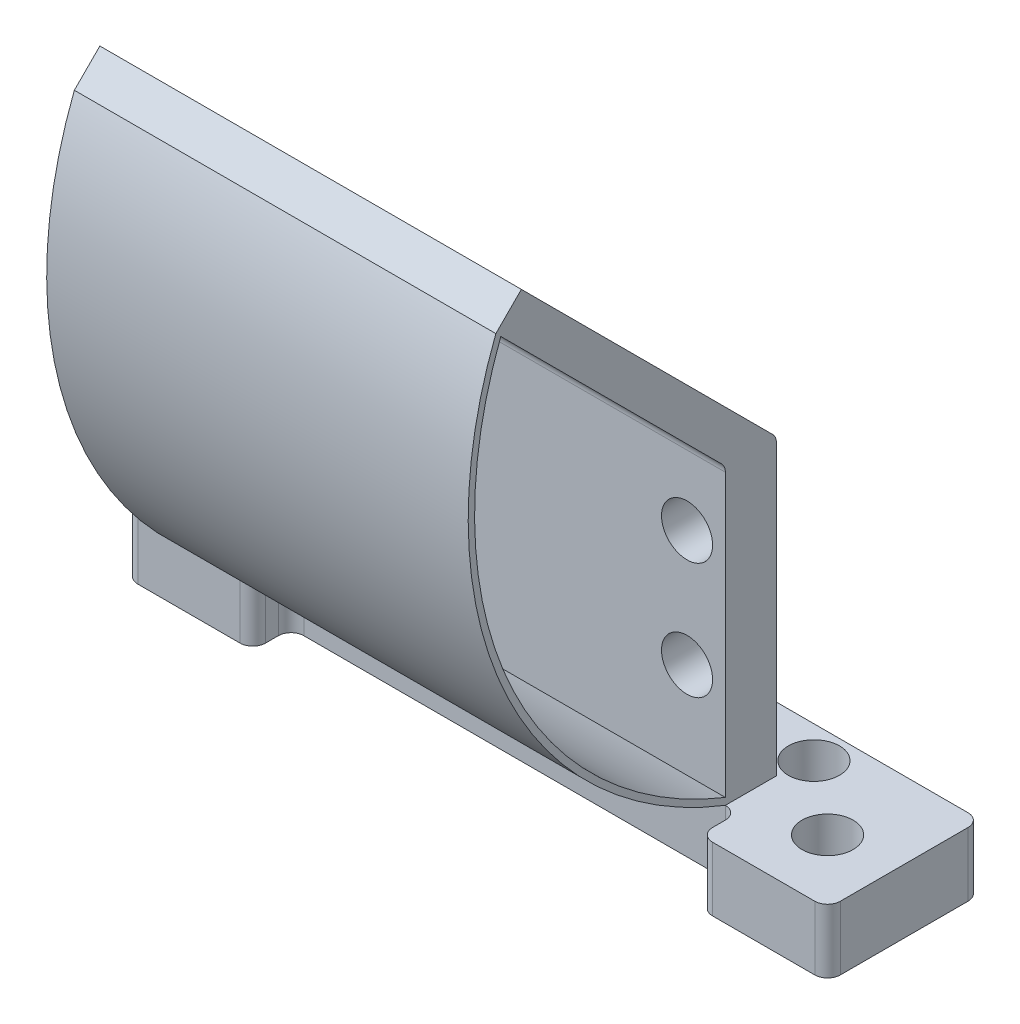
SolidWorks part; units mm, degrees
ref_plane "前视基准面" through (0, 0, 0) normal (0, 0, 1) x (1, 0, 0)
ref_plane "上视基准面" through (0, 0, 0) normal (0, 1, 0) x (1, 0, 0)
ref_plane "右视基准面" through (0, 0, 0) normal (1, 0, 0) x (0, 0, -1)
other "Configuration Table"
sketch "草图1" plane through (0, 0, 0) normal (0, 1, 0) x (1, 0, 0)
  line L0 (0.0338, 0) -> (0.0338, 2) construction
  line L2 (27.5338, -2.0074) -> (27.5338, 2.0025)
  line L4 (-27.4662, -1.9975) -> (-27.4662, 2.0025)
  line L5 (27.5338, -2.0074) -> (-27.4662, 2.0025) construction
  line L6 (27.5338, 2.0025) -> (-27.4662, -1.9975) construction
  line L7 (26.5338, -5) -> (18.5338, -5)
  line L8 (27.5338, -4) -> (27.5338, 4)
  line L9 (26.5338, 5) -> (18.5338, 5)
  line L10 (17.5338, -4) -> (17.5338, -3)
  line L11 (27.5338, -5) -> (17.5338, 5) construction
  line L12 (27.5338, 5) -> (17.5338, -5) construction
  line L13 (-26.4662, 5) -> (-18.4662, 5)
  line L14 (-17.4662, -4) -> (-17.4662, -3)
  line L15 (-26.4662, -5) -> (-18.4662, -5)
  line L16 (-27.4662, -4) -> (-27.4662, 4)
  line L17 (-17.4662, 3) -> (-17.4662, 4)
  line L18 (17.5338, 3) -> (17.5338, 4)
  line L19 (16.5338, -2) -> (-16.4662, -2)
  line L20 (16.5338, 2) -> (-16.4662, 2)
  arc A0 (18.5338, -5) -> (17.5338, -4) centre (18.5338, -4) cw
  arc A1 (26.5338, -5) -> (27.5338, -4) centre (26.5338, -4) ccw
  arc A2 (27.5338, 4) -> (26.5338, 5) centre (26.5338, 4) ccw
  arc A3 (18.5338, 5) -> (17.5338, 4) centre (18.5338, 4) ccw
  arc A4 (-18.4662, 5) -> (-17.4662, 4) centre (-18.4662, 4) cw
  arc A5 (-18.4662, -5) -> (-17.4662, -4) centre (-18.4662, -4) ccw
  arc A6 (-26.4662, -5) -> (-27.4662, -4) centre (-26.4662, -4) cw
  arc A7 (-27.4662, 4) -> (-26.4662, 5) centre (-26.4662, 4) cw
  arc A8 (-16.4662, -2) -> (-17.4662, -3) centre (-16.4662, -3) ccw
  arc A9 (-16.4662, 2) -> (-17.4662, 3) centre (-16.4662, 3) cw
  arc A10 (17.5338, 3) -> (16.5338, 2) centre (16.5338, 3) cw
  arc A11 (17.5338, -3) -> (16.5338, -2) centre (16.5338, -3) ccw
  point P0 (0, 0)
  point P6 (22.5338, 0)
  point P45 (-17.4662, 2)
  dimension "D6" = 1
  dimension "D7" = 1
  dimension "D1" = 55
  dimension "D2" = 4
  dimension "D3" = 5
  dimension "D4" = 10
  dimension "D5" = 10
extrude "凸台-拉伸2" add sketch "草图1" along normal blind 5 contours A11 L10 A0 L7 A1 L8 A2 L9 A3 L18 A10 L20 A9 L17 A4 L13 A7 L16 A6 L15 A5 L14 A8 L19
sketch "草图3" plane through (0, 0, 0) normal (0, -1, 0) x (1, 0, 0)
  line L0 (-16.4662, 2) -> (-16.4662, -2) construction
  line L1 (16.5338, 2) -> (16.5338, -2) construction
sketch "草图4" plane through (0, 5, 0) normal (0, 1, 0) x (1, 0, 0)
  line L0 (-16.4662, -2) -> (-16.4662, 2) construction
  line L1 (-16.4662, -2) -> (-16.4662, 2)
  line L2 (16.5338, -2) -> (16.5338, 2) construction
  line L3 (16.5338, -2) -> (-16.4662, -2) construction
  line L4 (16.5338, 2) -> (-16.4662, 2) construction
  line L5 (16.5338, -2) -> (16.5338, 2)
  line L6 (-16.4662, -2) -> (-16.4662, 2)
  line L7 (16.5338, -2) -> (-16.4662, -2)
  line L8 (16.5338, 2) -> (-16.4662, 2)
  line L10 (-16.4662, -2) -> (16.5338, -2)
  line L11 (-16.4662, -2) -> (-16.4662, 2)
  line L12 (-16.4662, -2) -> (16.5338, -2)
  line L13 (17.5338, -3) -> (17.5338, -4)
  line L14 (18.5338, -5) -> (26.5338, -5)
  line L15 (27.5338, -4) -> (27.5338, 4)
  line L16 (26.5338, 5) -> (18.5338, 5)
  line L17 (17.5338, 4) -> (17.5338, 3)
  line L18 (16.5338, 2) -> (-16.4662, 2)
  line L19 (-17.4662, 3) -> (-17.4662, 4)
  line L20 (-18.4662, 5) -> (-26.4662, 5)
  line L21 (-27.4662, 4) -> (-27.4662, -4)
  line L22 (-26.4662, -5) -> (-18.4662, -5)
  line L23 (-17.4662, -4) -> (-17.4662, -3)
  line L24 (-16.4662, -2) -> (16.5338, -2)
  line L25 (17.5338, -3) -> (17.5338, -4)
  line L26 (18.5338, -5) -> (26.5338, -5)
  line L27 (27.5338, -4) -> (27.5338, 4)
  line L28 (26.5338, 5) -> (18.5338, 5)
  line L29 (17.5338, 4) -> (17.5338, 3)
  line L30 (16.5338, 2) -> (-16.4662, 2)
  line L31 (-17.4662, 3) -> (-17.4662, 4)
  line L32 (-18.4662, 5) -> (-26.4662, 5)
  line L33 (-27.4662, 4) -> (-27.4662, -4)
  line L34 (-26.4662, -5) -> (-18.4662, -5)
  line L35 (-17.4662, -4) -> (-17.4662, -3)
  line L36 (-16.4662, 2) -> (16.5338, 2)
  line L37 (16.5338, -2) -> (16.5338, 2)
  arc A12 (17.5338, -3) -> (16.5338, -2) centre (16.5338, -3) ccw
  arc A13 (17.5338, -4) -> (18.5338, -5) centre (18.5338, -4) ccw
  arc A14 (26.5338, -5) -> (27.5338, -4) centre (26.5338, -4) ccw
  arc A15 (27.5338, 4) -> (26.5338, 5) centre (26.5338, 4) ccw
  arc A16 (18.5338, 5) -> (17.5338, 4) centre (18.5338, 4) ccw
  arc A17 (16.5338, 2) -> (17.5338, 3) centre (16.5338, 3) ccw
  arc A18 (-17.4662, 3) -> (-16.4662, 2) centre (-16.4662, 3) ccw
  arc A19 (-17.4662, 4) -> (-18.4662, 5) centre (-18.4662, 4) ccw
  arc A20 (-26.4662, 5) -> (-27.4662, 4) centre (-26.4662, 4) ccw
  arc A21 (-27.4662, -4) -> (-26.4662, -5) centre (-26.4662, -4) ccw
  arc A22 (-18.4662, -5) -> (-17.4662, -4) centre (-18.4662, -4) ccw
  arc A23 (-16.4662, -2) -> (-17.4662, -3) centre (-16.4662, -3) ccw
  arc A24 (17.5338, -3) -> (16.5338, -2) centre (16.5338, -3) ccw
  arc A25 (17.5338, -4) -> (18.5338, -5) centre (18.5338, -4) ccw
  arc A26 (26.5338, -5) -> (27.5338, -4) centre (26.5338, -4) ccw
  arc A27 (27.5338, 4) -> (26.5338, 5) centre (26.5338, 4) ccw
  arc A28 (18.5338, 5) -> (17.5338, 4) centre (18.5338, 4) ccw
  arc A29 (16.5338, 2) -> (17.5338, 3) centre (16.5338, 3) ccw
  arc A30 (-17.4662, 3) -> (-16.4662, 2) centre (-16.4662, 3) ccw
  arc A31 (-17.4662, 4) -> (-18.4662, 5) centre (-18.4662, 4) ccw
  arc A32 (-26.4662, 5) -> (-27.4662, 4) centre (-26.4662, 4) ccw
  arc A33 (-27.4662, -4) -> (-26.4662, -5) centre (-26.4662, -4) ccw
  arc A34 (-18.4662, -5) -> (-17.4662, -4) centre (-18.4662, -4) ccw
  arc A35 (-16.4662, -2) -> (-17.4662, -3) centre (-16.4662, -3) ccw
  dimension "D2" = 10
  dimension "D1" = 0
extrude "凸台-拉伸3" add sketch "草图4" along normal blind 23 contours L11 L10 L37 L36
sketch "草图5" plane through (-16.4662, 0, 0) normal (-1, 0, 0) x (0, 0, 1)
  line L0 (2.2929, 28.2929) -> (19.9706, 45.9706)
  line L1 (19.9706, 45.9706) -> (17.9706, 47.9706)
  line L2 (17.9706, 47.9706) -> (-1.7071, 28.2929)
  line L3 (2, 27.5858) -> (2, 5)
  line L4 (-2, 27.5858) -> (-2, 5)
  line L7 (-1.9102, 28) -> (-2, 28)
  line L8 (-2, 27.5858) -> (-2, 28)
  line L10 (-2, 5) -> (2, 5)
  line L11 (2, 5) -> (2, 28)
  line L12 (2, 28) -> (-2, 28)
  line L13 (-2, 28) -> (-2, 5)
  line L15 (2, 5) -> (2, 28)
  line L16 (2, 28) -> (-2, 28)
  line L17 (-2, 28) -> (-2, 5)
  arc A0 (2.2929, 28.2929) -> (2, 27.5858) centre (3, 27.5858) ccw
  arc A1 (-1.7071, 28.2929) -> (-2, 27.5858) centre (-1, 27.5858) ccw
  point P10 (2, 28)
  point P15 (-2, 28)
  line M5 (2, 5) -> (2, 28)
  line M6 (2, 28) -> (-2, 28)
  dimension "D1" = 1
  dimension "D2" = 1
  dimension "D3" = 0
extrude "凸台-拉伸4" add sketch "草图5" against normal blind 33 contours L2 A1 A0 L0 L1 M6 M5
sketch "草图11" plane through (0, 0, 2) normal (0, 0, 1) x (1, 0, 0)
  line L0 (-12.7501, 22.1431) -> (-12.7501, 13.0285) construction
  line L1 (-11.034, 22.1431) -> (-11.034, 13.0285)
  line L2 (-14.4662, 22.1431) -> (-14.4662, 13.0285)
  line L3 (16.5338, 27.5858) -> (-16.4662, 27.5858) construction
  line L4 (-16.4662, 27.5858) -> (-16.4662, 5) construction
  line L5 (-12.7501, 22.1431) -> (10.7248, 22.1431) construction
  line L6 (-12.7501, 13.0285) -> (13.887, 13.0285) construction
  line L7 (16.5338, 27.5858) -> (16.5338, 5) construction
  arc A0 (-11.034, 22.1431) -> (-14.4662, 22.1431) centre (-12.7501, 22.1431) ccw
  arc A1 (-14.4662, 13.0285) -> (-11.034, 13.0285) centre (-12.7501, 13.0285) ccw
  circle A2 centre (13.5338, 22.1431) radius 2
  circle A3 centre (13.5338, 13.0285) radius 2
  point P2 (-12.7501, 17.5858)
  dimension "D5" = 4
  dimension "D6" = 4
  dimension "D1" = 10
  dimension "D2" = 2
  dimension "D3" = 3
  dimension "D4" = 3
sketch "草图13" plane through (0, 0, 2) normal (0, 0, 1) x (1, 0, 0)
extrude "切除-拉伸1" cut sketch "草图11" against normal blind 14 contours L2 A1 L1 A0 | A2 | A3
sketch "草图14" plane through (0, 0, 2) normal (0, 0, 1) x (1, 0, 0)
sketch "草图15" plane through (0, 0, 2) normal (0, 0, 1) x (1, 0, 0)
sketch "草图16" plane through (-16.4662, 0, 0) normal (-1, 0, 0) x (0, 0, 1)
  line L1 (-2, 28) -> (-2, 5) construction
  line L2 (-2, 27.5858) -> (-2, 28) construction
  line L3 (17.9706, 47.9706) -> (-1.7071, 28.2929) construction
  line L4 (19.9706, 45.9706) -> (17.9706, 47.9706) construction
  line L5 (2.2929, 28.2929) -> (19.9706, 45.9706) construction
  line L6 (2, 27.5858) -> (2, 5) construction
  line L7 (2, 5) -> (2, 28) construction
  line L8 (2, 28) -> (-2, 28) construction
  line L9 (-1.9102, 28) -> (-2, 28) construction
  line L11 (-2, 28) -> (-2, 27.5858)
  line L12 (-2, 27.5858) -> (-2, 28)
  line L13 (17.9706, 47.9706) -> (-1.7071, 28.2929)
  line L14 (19.9706, 45.9706) -> (17.9706, 47.9706)
  line L15 (2.2929, 28.2929) -> (19.9706, 45.9706)
  line L16 (2, 27.5858) -> (2, 5)
  line L17 (2, 5) -> (2, 28)
  line L18 (-1.9102, 28) -> (-2, 28)
  line L19 (-1.9102, 28) -> (-2, 28)
  arc A0 (-1.7071, 28.2929) -> (-2, 27.5858) centre (-1, 27.5858) ccw construction
  arc A1 (2.2929, 28.2929) -> (2, 27.5858) centre (3, 27.5858) ccw construction
  arc A2 (-1.9102, 28) -> (-2, 27.5858) centre (-1, 27.5858) ccw
  arc A3 (2.2929, 28.2929) -> (2, 27.5858) centre (3, 27.5858) ccw
  line M7 (-1.9102, 28) -> (-2, 28)
  line M8 (-2, 28) -> (-2, 5)
extrude "切除-拉伸2" cut sketch "草图16" against normal up to surface (33 mm away) contours A2 M7 M8 up to face at (16.5338, 27.1279, 4.0593)
sketch "草图17" plane through (0, 5, 0) normal (0, 1, 0) x (1, 0, 0)
  line L0 (-27.4662, -4) -> (-27.4662, 4) construction
  line L1 (-26.4662, -5) -> (-18.4662, -5) construction
  line L6 (16.5338, 2) -> (16.5338, -2)
  line L7 (17.5338, -3) -> (17.5338, -4)
  line L8 (18.5338, -5) -> (26.5338, -5)
  line L9 (27.5338, -4) -> (27.5338, 4)
  line L10 (26.5338, 5) -> (18.5338, 5)
  line L11 (17.5338, 4) -> (17.5338, 3)
  line L12 (16.5338, 2) -> (16.5338, -2)
  line L13 (17.5338, -3) -> (17.5338, -4)
  line L14 (18.5338, -5) -> (26.5338, -5)
  line L15 (27.5338, -4) -> (27.5338, 4)
  line L16 (26.5338, 5) -> (18.5338, 5)
  line L17 (17.5338, 4) -> (17.5338, 3)
  circle A0 centre (22.5338, 0) radius 2
  circle A1 centre (-22.4662, 0) radius 2
  arc A6 (17.5338, -3) -> (16.5338, -2) centre (16.5338, -3) ccw
  arc A7 (17.5338, -4) -> (18.5338, -5) centre (18.5338, -4) ccw
  arc A8 (26.5338, -5) -> (27.5338, -4) centre (26.5338, -4) ccw
  arc A9 (27.5338, 4) -> (26.5338, 5) centre (26.5338, 4) ccw
  arc A10 (18.5338, 5) -> (17.5338, 4) centre (18.5338, 4) ccw
  arc A11 (16.5338, 2) -> (17.5338, 3) centre (16.5338, 3) ccw
  arc A12 (17.5338, -3) -> (16.5338, -2) centre (16.5338, -3) ccw
  arc A13 (17.5338, -4) -> (18.5338, -5) centre (18.5338, -4) ccw
  arc A14 (26.5338, -5) -> (27.5338, -4) centre (26.5338, -4) ccw
  arc A15 (27.5338, 4) -> (26.5338, 5) centre (26.5338, 4) ccw
  arc A16 (18.5338, 5) -> (17.5338, 4) centre (18.5338, 4) ccw
  arc A17 (16.5338, 2) -> (17.5338, 3) centre (16.5338, 3) ccw
  dimension "D4" = 4
  dimension "D7" = 4
  dimension "D2" = 5
  dimension "D3" = 5
  dimension "D5" = 5
  dimension "D6" = 5
  dimension "D1" = 0
extrude "切除-拉伸3" cut sketch "草图17" against normal up to surface (5 mm away) contours A0 | A1 up to face at (0.0338, 0, 0)
sketch "草图18" plane through (0, 0, 0) normal (0, -1, 0) x (1, 0, 0)
  line L1 (-18.4662, -5) -> (18.5338, -5)
  line L2 (-18.4662, -5) -> (-18.4662, -2)
  line L3 (-18.4662, -2) -> (18.5338, -2)
  line L4 (18.5338, -5) -> (18.5338, -2)
  line L12 (16.5338, 2) -> (-16.4662, 2)
  line L13 (-17.4662, 3) -> (-17.4662, 4)
  line L14 (-18.4662, 5) -> (-26.4662, 5)
  line L15 (-27.4662, 4) -> (-27.4662, -4)
  line L16 (-26.4662, -5) -> (-18.4662, -5)
  line L17 (-17.4662, -4) -> (-17.4662, -3)
  line L18 (-16.4662, -2) -> (16.5338, -2)
  line L19 (17.5338, -3) -> (17.5338, -4)
  line L20 (18.5338, -5) -> (26.5338, -5)
  line L21 (27.5338, -4) -> (27.5338, 4)
  line L22 (26.5338, 5) -> (18.5338, 5)
  line L23 (17.5338, 4) -> (17.5338, 3)
  line L24 (16.5338, 2) -> (-16.4662, 2)
  line L25 (-17.4662, 3) -> (-17.4662, 4)
  line L26 (-18.4662, 5) -> (-26.4662, 5)
  line L27 (-27.4662, 4) -> (-27.4662, -4)
  line L28 (-26.4662, -5) -> (-18.4662, -5)
  line L29 (-17.4662, -4) -> (-17.4662, -3)
  line L30 (-16.4662, -2) -> (16.5338, -2)
  line L31 (17.5338, -3) -> (17.5338, -4)
  line L32 (18.5338, -5) -> (26.5338, -5)
  line L33 (27.5338, -4) -> (27.5338, 4)
  line L34 (26.5338, 5) -> (18.5338, 5)
  line L35 (17.5338, 4) -> (17.5338, 3)
  arc A12 (-17.4662, 3) -> (-16.4662, 2) centre (-16.4662, 3) ccw
  arc A13 (-17.4662, 4) -> (-18.4662, 5) centre (-18.4662, 4) ccw
  arc A14 (-26.4662, 5) -> (-27.4662, 4) centre (-26.4662, 4) ccw
  arc A15 (-27.4662, -4) -> (-26.4662, -5) centre (-26.4662, -4) ccw
  arc A16 (-18.4662, -5) -> (-17.4662, -4) centre (-18.4662, -4) ccw
  arc A17 (-16.4662, -2) -> (-17.4662, -3) centre (-16.4662, -3) ccw
  arc A18 (17.5338, -3) -> (16.5338, -2) centre (16.5338, -3) ccw
  arc A19 (17.5338, -4) -> (18.5338, -5) centre (18.5338, -4) ccw
  arc A20 (26.5338, -5) -> (27.5338, -4) centre (26.5338, -4) ccw
  arc A21 (27.5338, 4) -> (26.5338, 5) centre (26.5338, 4) ccw
  arc A22 (18.5338, 5) -> (17.5338, 4) centre (18.5338, 4) ccw
  arc A23 (16.5338, 2) -> (17.5338, 3) centre (16.5338, 3) ccw
  arc A24 (-17.4662, 3) -> (-16.4662, 2) centre (-16.4662, 3) ccw
  arc A25 (-17.4662, 4) -> (-18.4662, 5) centre (-18.4662, 4) ccw
  arc A26 (-26.4662, 5) -> (-27.4662, 4) centre (-26.4662, 4) ccw
  arc A27 (-27.4662, -4) -> (-26.4662, -5) centre (-26.4662, -4) ccw
  arc A28 (-18.4662, -5) -> (-17.4662, -4) centre (-18.4662, -4) ccw
  arc A29 (-16.4662, -2) -> (-17.4662, -3) centre (-16.4662, -3) ccw
  arc A30 (17.5338, -3) -> (16.5338, -2) centre (16.5338, -3) ccw
  arc A31 (17.5338, -4) -> (18.5338, -5) centre (18.5338, -4) ccw
  arc A32 (26.5338, -5) -> (27.5338, -4) centre (26.5338, -4) ccw
  arc A33 (27.5338, 4) -> (26.5338, 5) centre (26.5338, 4) ccw
  arc A34 (18.5338, 5) -> (17.5338, 4) centre (18.5338, 4) ccw
  arc A35 (16.5338, 2) -> (17.5338, 3) centre (16.5338, 3) ccw
  dimension "D1" = 0
extrude "凸台-拉伸5" add sketch "草图18" against normal blind 5 contours L2 L1 L4 L3
sketch "草图19" plane through (0, 0, 0) normal (0, -1, 0) x (1, 0, 0)
  line L0 (-27.4662, 4) -> (-27.4662, -4) construction
  line L1 (-27.4662, -2.8293) -> (27.5338, -2.8293)
  line L2 (-27.4662, -2.8293) -> (-27.4662, -7)
  line L3 (-27.4662, -7) -> (27.5338, -7)
  line L4 (27.5338, -2.8293) -> (27.5338, -7)
  line L5 (-16.4662, -2) -> (16.5338, -2) construction
  line L6 (-16.4662, -2) -> (16.5338, -2)
  dimension "D1" = 55
  dimension "D2" = 5
extrude "凸台-拉伸6" add sketch "草图19" against normal blind 5 contours L2 L1 L4 L3
sketch "草图21" plane through (0, 0, 0) normal (0, -1, 0) x (1, 0, 0)
  line L0 (-27.4662, -7) -> (27.5338, -7) construction
  line L1 (-16.4662, -2) -> (16.5338, -2) construction
  line L2 (-27.4662, -7) -> (27.5338, -7)
  line L3 (-16.4662, -2) -> (16.5338, -2)
  line L4 (0, 0) -> (0, 7.758) construction
  line L8 (-27.4662, -7) -> (27.5338, -7)
  line L9 (27.5338, -7) -> (27.5338, 4)
  line L10 (26.5338, 5) -> (18.5338, 5)
  line L11 (17.5338, 4) -> (17.5338, 3)
  line L12 (16.5338, 2) -> (-16.4662, 2)
  line L13 (-17.4662, 3) -> (-17.4662, 4)
  line L14 (-18.4662, 5) -> (-26.4662, 5)
  line L15 (-27.4662, 4) -> (-27.4662, -7)
  line L16 (-27.4662, -7) -> (27.5338, -7)
  line L17 (27.5338, -7) -> (27.5338, 4)
  line L18 (26.5338, 5) -> (18.5338, 5)
  line L19 (17.5338, 4) -> (17.5338, 3)
  line L20 (16.5338, 2) -> (-16.4662, 2)
  line L21 (-17.4662, 3) -> (-17.4662, 4)
  line L22 (-18.4662, 5) -> (-26.4662, 5)
  line L23 (-27.4662, 4) -> (-27.4662, -7)
  circle A0 centre (-16.9662, -4.5) radius 2
  circle A1 centre (16.9662, -4.5) radius 2
  arc A6 (27.5338, 4) -> (26.5338, 5) centre (26.5338, 4) ccw
  arc A7 (18.5338, 5) -> (17.5338, 4) centre (18.5338, 4) ccw
  arc A8 (16.5338, 2) -> (17.5338, 3) centre (16.5338, 3) ccw
  arc A9 (-17.4662, 3) -> (-16.4662, 2) centre (-16.4662, 3) ccw
  arc A10 (-17.4662, 4) -> (-18.4662, 5) centre (-18.4662, 4) ccw
  arc A11 (-26.4662, 5) -> (-27.4662, 4) centre (-26.4662, 4) ccw
  arc A12 (27.5338, 4) -> (26.5338, 5) centre (26.5338, 4) ccw
  arc A13 (18.5338, 5) -> (17.5338, 4) centre (18.5338, 4) ccw
  arc A14 (16.5338, 2) -> (17.5338, 3) centre (16.5338, 3) ccw
  arc A15 (-17.4662, 3) -> (-16.4662, 2) centre (-16.4662, 3) ccw
  arc A16 (-17.4662, 4) -> (-18.4662, 5) centre (-18.4662, 4) ccw
  arc A17 (-26.4662, 5) -> (-27.4662, 4) centre (-26.4662, 4) ccw
  dimension "D2" = 4
  dimension "D3" = 2.5
  dimension "D4" = 10.5
  dimension "D1" = 0
extrude "切除-拉伸4" cut sketch "草图21" against normal up to surface (5 mm away) contours A0 | A1 up to face at (0.0338, 5, 1.7759)
fillet "圆角1" radius 1 2 edges at (27.5338, 2.5, -7) (-27.4662, 2.5, -7)
sketch "草图29" plane through (16.5338, 0, 0) normal (1, 0, 0) x (0, 0, -1)
  line L0 (-2, 5.5374) -> (-2, 5)
  line L1 (-2, 27.5858) -> (-2, 5) construction
  line L2 (-19.9706, 45.9706) -> (-19.5839, 45.5839)
  line L3 (-2.2929, 28.2929) -> (-19.9706, 45.9706) construction
  arc A0 (-19.9706, 45.9706) -> (-2, 5) centre (9.5, 34.4706) ccw
  arc A1 (-19.5048, 45.7888) -> (-1.8182, 5.4658) centre (9.5, 34.4706) ccw
  arc A2 (-2, 5.5374) -> (-19.5839, 45.5839) centre (9.5, 34.4706) cw
  dimension "D1" = 0.5
extrude "凸台-拉伸10" add sketch "草图29" against normal up to surface (33 mm away) contours A2 L2 A0 L0 up to face at (-16.4662, 26.9696, 4.7983)
